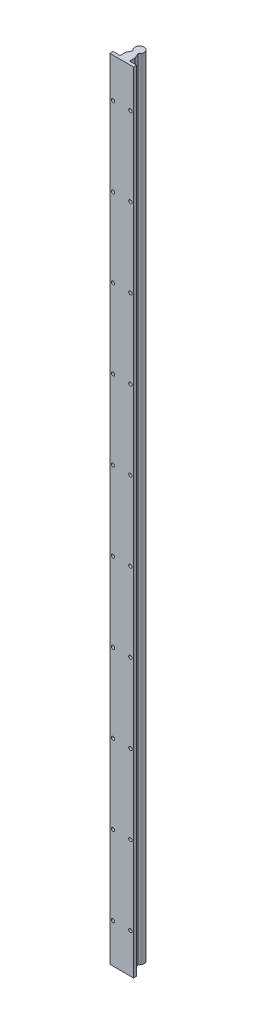
SolidWorks part; units mm, degrees
ref_plane "Front Plane" through (0, 0, 0) normal (0, 0, 1) x (1, 0, 0)
ref_plane "Top Plane" through (0, 0, 0) normal (0, 1, 0) x (1, 0, 0)
ref_plane "Right Plane" through (0, 0, 0) normal (1, 0, 0) x (0, 0, -1)
sketch "Sketch1" plane through (0, 0, 0) normal (0, 1, 0) x (1, 0, 0)
  line L0 (0, 0) -> (0, -20.5) construction
  line L1 (15, -22.5) -> (-15, -22.5)
  line L2 (15, -22.5) -> (15, -18.5)
  line L3 (15, -18.5) -> (6, -18.5)
  line L4 (-15, -22.5) -> (-15, -18.5)
  line L5 (15, -22.5) -> (-15, -18.5) construction
  line L6 (15, -18.5) -> (-15, -22.5) construction
  line L7 (-6, -11.5) -> (-3.25, -5.0436)
  line L8 (-6, -18.5) -> (-6, -11.5)
  line L9 (6, -18.5) -> (6, -11.5)
  line L10 (3.25, -5.0436) -> (6, -11.5)
  line L11 (-6, -18.5) -> (-15, -18.5)
  arc A0 (3.25, -5.0436) -> (-3.25, -5.0436) centre (0, 0) ccw
  point P3 (0, -20.5)
  point P14 (-3.25, -5.0436)
  point P16 (3.25, -5.0436)
  dimension "D1" = 12
  dimension "D2" = 4
  dimension "D3" = 22.5
  dimension "D4" = 30
  dimension "D6" = 12
  dimension "D7" = 7
  dimension "D8" = 6.5
extrude "Boss-Extrude1" add sketch "Sketch1" along normal blind 1000
sketch "Sketch2" plane through (0, 0, 18.5) normal (0, 0, -1) x (-1, 0, 0)
  line L0 (0, 0) -> (0, 50000) construction
  line L1 (6, 1000) -> (-6, 1000) construction
  line L2 (6, 1000) -> (15, 1000) construction
  circle A0 centre (-11, 950) radius 2.125
  circle A1 centre (11, 950) radius 2.125
  point P5 (0, 0)
  point P9 (0, 1000)
  dimension "D1" = 4.25
  dimension "D2" = 22
  dimension "D3" = 50
extrude "Cut-Extrude1" cut sketch "Sketch2" against normal through all
pattern_linear "LPattern1" count 10 spacing 100 along (0, -1, 0) of "Cut-Extrude1"
